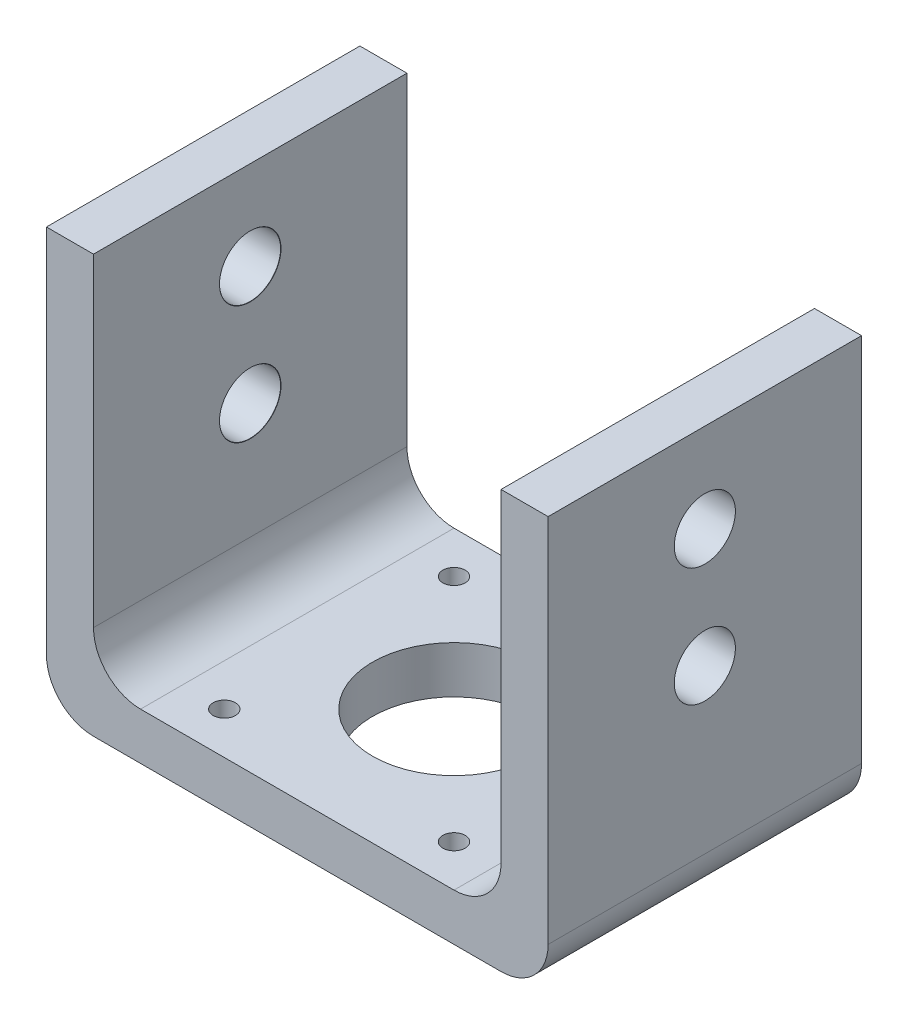
SolidWorks part; units mm, degrees
ref_plane "Front Plane" through (0, 0, 0) normal (0, 0, 1) x (1, 0, 0)
ref_plane "Top Plane" through (0, 0, 0) normal (0, 1, 0) x (1, 0, 0)
ref_plane "Right Plane" through (0, 0, 0) normal (1, 0, 0) x (0, 0, -1)
sketch "Sketch1" plane through (0, 0, 0) normal (0, 1, 0) x (1, 0, 0)
  line L1 (0, 0) -> (42.3, 0)
  line L2 (0, 0) -> (0, -42.3)
  line L3 (0, -42.3) -> (42.3, -42.3)
  line L4 (42.3, 0) -> (42.3, -42.3)
  dimension "D1" = 42.3
  dimension "D2" = 42.3
  dimension "D3" = 0
  dimension "D4" = 0
extrude "Boss-Extrude1" add sketch "Sketch1" along normal blind 6.35
sketch "Sketch2" plane through (0, 6.35, 0) normal (0, 1, 0) x (1, 0, 0)
  line L0 (0, 0) -> (0, -42.3) construction
  line L1 (42.3, 0) -> (0, 0) construction
  line L3 (42.3, -42.3) -> (42.3, 0) construction
  circle A0 centre (21.15, -21.15) radius 11
  circle A1 centre (5.65, -5.65) radius 1.5
  circle A2 centre (5.65, -36.65) radius 1.5
  circle A3 centre (36.65, -5.65) radius 1.5
  circle A4 centre (36.65, -36.65) radius 1.5
  point P16 (0, -8.0372)
  point P17 (0, -9.377)
  dimension "D3" = 22
  dimension "D4" = 3
  dimension "D5" = 3
  dimension "D6" = 3
  dimension "D7" = 3
  dimension "D12" = 5.65
  dimension "D1" = 21.15
  dimension "D2" = 21.15
  dimension "D8" = 31
  dimension "D9" = 31
  dimension "D10" = 31
  dimension "D11" = 31
  dimension "D13" = 5.65
  dimension "D14" = 5.65
  dimension "D15" = 5.65
extrude "Cut-Extrude1" cut sketch "Sketch2" against normal blind 6.35
sketch "Sketch3" plane through (42.3, 0, 0) normal (1, 0, 0) x (0, 0, -1)
  line L0 (-42.3, 6.35) -> (-42.3, 0) construction
  line L1 (-42.3, 6.35) -> (0, 6.35)
  line L2 (-42.3, 6.35) -> (-42.3, 0)
  line L3 (-42.3, 0) -> (0, 0)
  line L4 (0, 6.35) -> (0, 0)
  line L5 (-42.3, 6.35) -> (0, 6.35) construction
  line L6 (0, 6.35) -> (0, 0) construction
  line L7 (-42.3, 0) -> (0, 0) construction
  dimension "D1" = 0
  dimension "D2" = 0
  dimension "D3" = 0
  dimension "D4" = 0
extrude "Boss-Extrude2" add sketch "Sketch3" along normal blind 12.7
sketch "Sketch4" plane through (0, 6.35, 0) normal (0, 1, 0) x (1, 0, 0)
  line L0 (55, 0) -> (55, -42.3) construction
  line L1 (48.65, 0) -> (55, 0)
  line L2 (48.65, 0) -> (48.65, -42.3)
  line L3 (48.65, -42.3) -> (55, -42.3)
  line L4 (55, 0) -> (55, -42.3)
  line L5 (0, -42.3) -> (55, -42.3) construction
  line L6 (55, 0) -> (0, 0) construction
  dimension "D1" = 0
  dimension "D2" = 0
  dimension "D3" = 0
  dimension "D4" = 6.35
extrude "Boss-Extrude3" add sketch "Sketch4" along normal blind 50
fillet "Fillet1" radius 6.35 1 edges at (48.65, 6.35, 21.15)
fillet "Fillet2" radius 6.35 1 edges at (55, 0, 21.15)
hole_wizard "Tap Drill for M8 Helicoil1" positions "Sketch7" profile "Sketch8" hole size "M8x1.0" standard "ANSI Metric"
sketch "Sketch7" plane through (48.65, 0, 0) normal (-1, 0, 0) x (0, 0, 1)
  line L0 (0, 56.35) -> (42.3, 56.35) construction
  line L1 (42.3, 56.35) -> (42.3, 12.7) construction
  point P0 (21.15, 44.35)
  point P2 (21.15, 28.35)
  dimension "D1" = 12
  dimension "D2" = 21.15
  dimension "D3" = 21.15
  dimension "D4" = 16
sketch "Sketch8" plane through (48.65, 44.35, 21.15) normal (0, 1, 0) x (0, 0, 1)
  line L0 (0, 0) -> (0, 6.35)
  line L1 (0, 6.35) -> (4.125, 6.35)
  line L2 (4.125, 6.35) -> (4.125, 0.025)
  line L3 (4.125, 0.025) -> (4.15, 0)
  line L5 (4.15, 0) -> (0, 0)
  line L6 (-4.125, 0.025) -> (-4.15, 0) construction
  line L11 (0, -6.35) -> (0, 107.95) construction
  dimension "Thru Hole Dia." = 8.25
  dimension "Thru Hole Depth" = 6.35
  dimension "Near C'Sink Dia." = 8.3
  dimension "Near C'Sink Angle" = 90
ref_plane "Plane1" through (21.15, 0, 0) normal (-1, 0, 0) x (0, 0, 1)
mirror "Mirror4" about plane through (21.15, 0, 0) normal (-1, 0, 0) of "Boss-Extrude2", "Fillet1", "Fillet2", "Tap Drill for M8 Helicoil1", "Boss-Extrude3"
